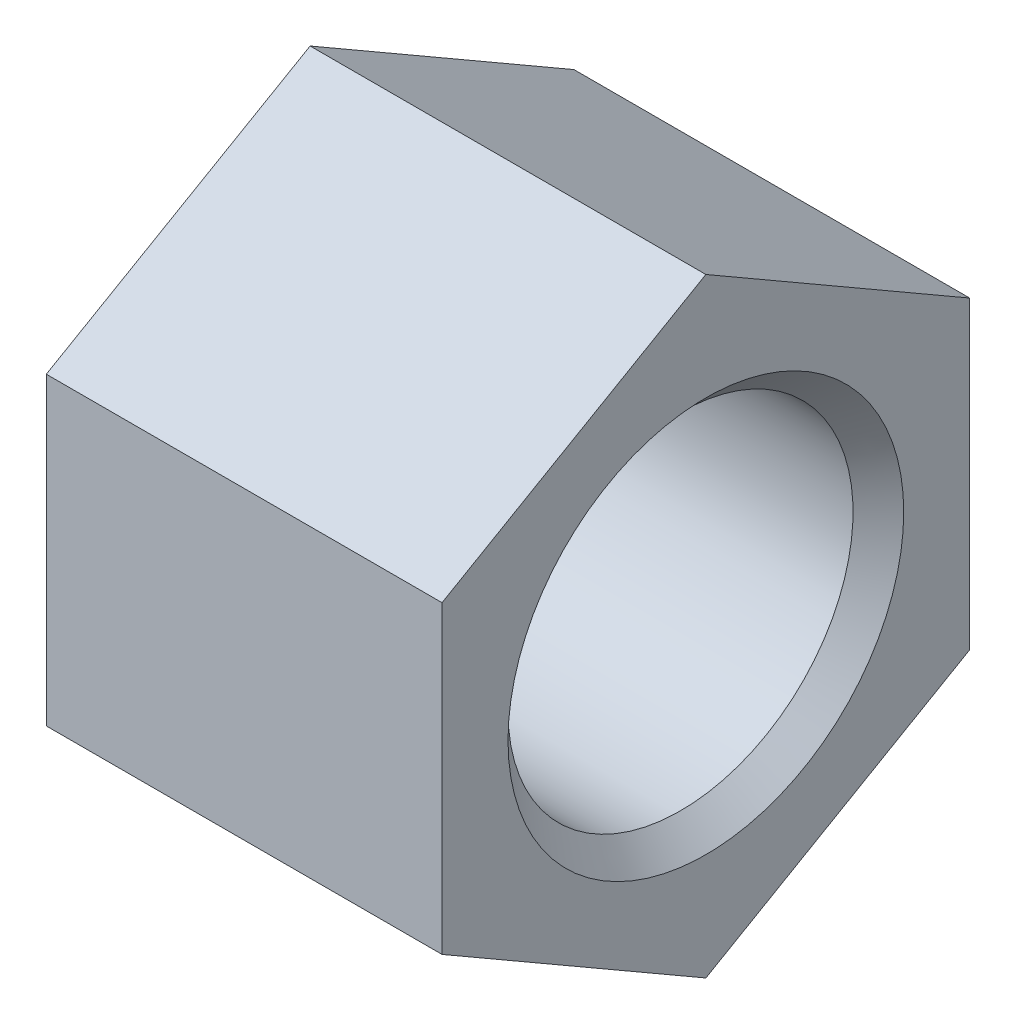
SolidWorks part; units mm, degrees
material "Сталь"
ref_plane "Спереди" through (0, 0, 0) normal (0, 0, 1) x (1, 0, 0)
ref_plane "Сверху" through (0, 0, 0) normal (0, 1, 0) x (1, 0, 0)
ref_plane "Справа" through (0, 0, 0) normal (1, 0, 0) x (0, 0, -1)
sketch "Эскиз1" plane through (0, 0, 0) normal (0, 0, 1) x (1, 0, 0)
  line L0 (0, 6.5) -> (5, 6.5)
  line L1 (5, 6.5) -> (5, 15)
  line L2 (5, 15) -> (10, 15)
  line L3 (10, 15) -> (10, 13.079)
  line L4 (10, 13.079) -> (30, 13.079)
  line L5 (30, 13.079) -> (30, 19.5)
  line L6 (30, 19.5) -> (0, 19.5)
  line L7 (0, 19.5) -> (0, 6.5)
  line L8 (0, 0) -> (25.6625, 0) construction
  dimension "D1" = 39
  dimension "D2" = 13
  dimension "D3" = 5
  dimension "D4" = 30
  dimension "D5" = 30
  dimension "D6" = 26.158
  dimension "D7" = 20
revolve "Повернуть1" add sketch "Эскиз1" angle 360 about L8
cosmetic thread "Условное изображение резьбы1" parameters "D2"=30
chamfer "Фаска1" distance 1.921 angle 45 1 edges at (30, 0, 13.079)
sketch "Эскиз2" plane through (30, 0, 0) normal (1, 0, 0) x (0, 0, -1)
  line L1 (0, 23.094) -> (-20, 11.547)
  line L2 (-20, 11.547) -> (-20, -11.547)
  line L3 (-20, -11.547) -> (0, -23.094)
  line L4 (0, -23.094) -> (20, -11.547)
  line L5 (20, -11.547) -> (20, 11.547)
  line L6 (20, 11.547) -> (0, 23.094)
  circle A0 centre (0, 0) radius 20 construction
  circle A1 centre (0, 0) radius 19.5
  circle A2 centre (0, 0) radius 19.5
  dimension "D2" = 40
  dimension "D1" = 0
extrude "Бобышка-Вытянуть1" add sketch "Эскиз2" against normal up to surface (30 mm away) up to face at (0, 0, 6.5)
